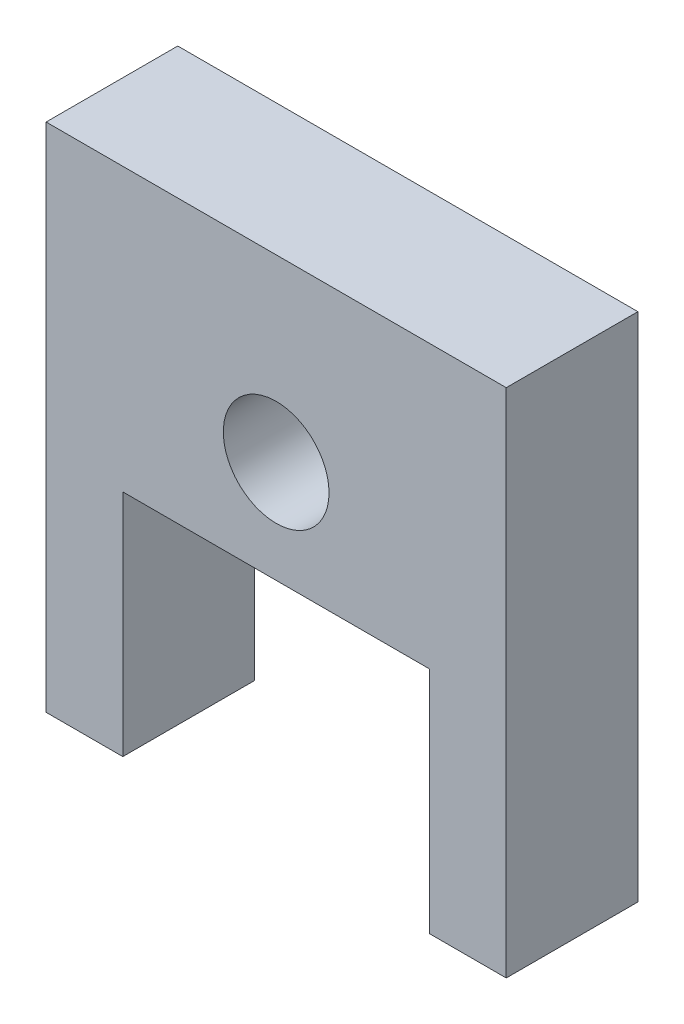
SolidWorks part; units mm, degrees
ref_plane "Front Plane" through (0, 0, 0) normal (0, 0, 1) x (1, 0, 0)
ref_plane "Top Plane" through (0, 0, 0) normal (0, 1, 0) x (1, 0, 0)
ref_plane "Right Plane" through (0, 0, 0) normal (1, 0, 0) x (0, 0, -1)
sketch "Sketch1" plane through (0, 0, 0) normal (0, 0, 1) x (1, 0, 0)
  line L0 (2.75, 0) -> (-2.75, 0) construction
  line L1 (0, 0) -> (3, 0)
  line L2 (18, 0) -> (18, 20)
  line L3 (18, 20) -> (0, 20)
  line L4 (0, -2.75) -> (0, 2.75) construction
  line L5 (0, 20) -> (0, 0)
  line L6 (3, 0) -> (3, 8.97)
  line L7 (3, 8.97) -> (15, 8.97)
  line L8 (15, 8.97) -> (15, 0)
  line L9 (15, 0) -> (18, 0)
  dimension "D1" = 18
  dimension "D2" = 20
  dimension "D3" = 12
  dimension "D4" = 3
  dimension "D5" = 8.97
extrude "Boss-Extrude1" add sketch "Sketch1" along normal blind 5.15
sketch "Sketch3" plane through (0, 0, 5.15) normal (0, 0, 1) x (1, 0, 0)
  line L0 (9, 8.97) -> (9, 22.3726) construction
  line L1 (3, 8.97) -> (15, 8.97) construction
  circle A0 centre (9, 12.97) radius 2.0675
  dimension "D1" = 4
extrude "Cut-Extrude1" cut sketch "Sketch3" against normal through all
